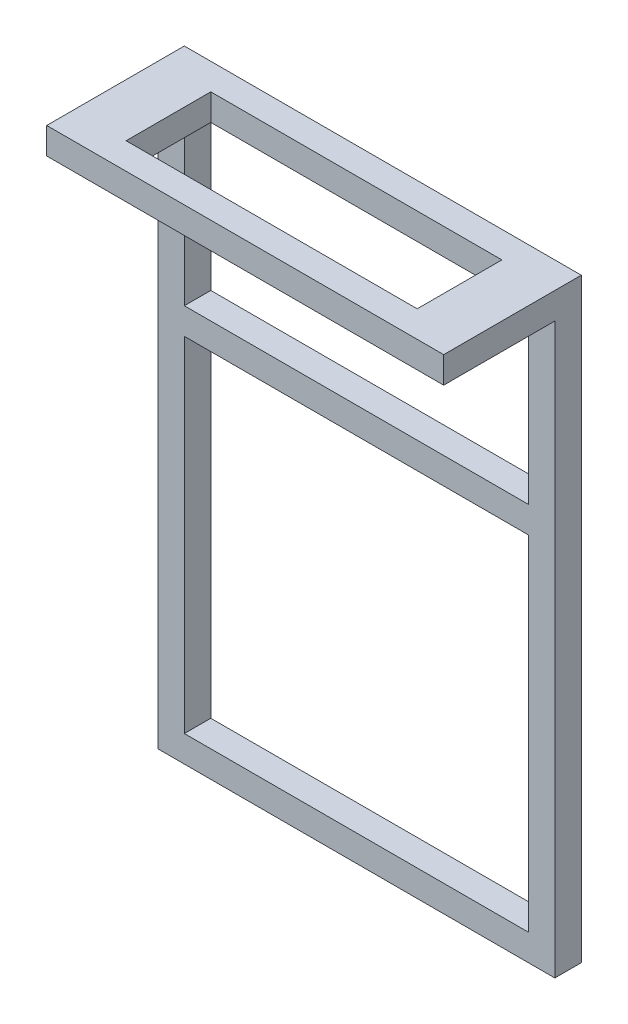
SolidWorks part; units mm, degrees
ref_plane "Front Plane" through (0, 0, 0) normal (0, 0, 1) x (1, 0, 0)
ref_plane "Top Plane" through (0, 0, 0) normal (0, 1, 0) x (1, 0, 0)
ref_plane "Right Plane" through (0, 0, 0) normal (1, 0, 0) x (0, 0, -1)
sketch "Sketch1" plane through (0, 0, 0) normal (0, 1, 0) x (1, 0, 0)
  line L1 (0, 0) -> (30, 0)
  line L2 (0, 0) -> (0, -10.4)
  line L3 (0, -10.4) -> (30, -10.4)
  line L4 (30, 0) -> (30, -10.4)
  dimension "D1" = 10.4
  dimension "D2" = 30
extrude "Boss-Extrude1" add sketch "Sketch1" along normal blind 2
sketch "Sketch2" plane through (0, 2, 0) normal (0, 1, 0) x (1, 0, 0)
  line L0 (0, 0) -> (0, -10.4) construction
  line L1 (4, -2) -> (26, -2)
  line L2 (4, -2) -> (4, -8.4)
  line L3 (4, -8.4) -> (26, -8.4)
  line L4 (26, -2) -> (26, -8.4)
  line L5 (30, -10.4) -> (30, 0) construction
  line L6 (30, 0) -> (0, 0) construction
  line L7 (0, -10.4) -> (30, -10.4) construction
  dimension "D1" = 4
  dimension "D2" = 4
  dimension "D3" = 2
  dimension "D4" = 2
extrude "Cut-Extrude1" cut sketch "Sketch2" against normal through all
sketch "Sketch4" plane through (0, 2, 0) normal (0, 1, 0) x (1, 0, 0)
  line L0 (30, -10.4) -> (30, 0) construction
  line L1 (0, 0) -> (30, 0)
  line L2 (0, 0) -> (0, -2)
  line L3 (0, -2) -> (30, -2)
  line L4 (30, 0) -> (30, -2)
  line L5 (26, -2) -> (4, -2) construction
extrude "Boss-Extrude2" add sketch "Sketch4" against normal blind 45
sketch "Sketch5" plane through (0, 0, 0) normal (0, 0, -1) x (-1, 0, 0)
  line L0 (-30, 2) -> (-30, -43) construction
  line L1 (-30, -13) -> (0, -13)
  line L2 (-30, -13) -> (-30, -43)
  line L3 (-30, -43) -> (0, -43)
  line L4 (0, -13) -> (0, -43)
  line L5 (-28, -15) -> (-28, -41)
  line L6 (-28, -41) -> (-2, -41)
  line L7 (-2, -15) -> (-2, -41)
  line L8 (-28, -15) -> (-2, -15)
  dimension "D1" = 30
  dimension "D2" = 2
extrude "Cut-Extrude3" cut sketch "Sketch5" against normal through all contours L8 L5 L6 L7
sketch "Sketch6" plane through (0, 0, 0) normal (0, 0, -1) x (-1, 0, 0)
  line L0 (-28, -15) -> (-2, -15) construction
  line L1 (-28, 0) -> (-2, 0)
  line L2 (-28, 0) -> (-28, -13)
  line L3 (-28, -13) -> (-2, -13)
  line L4 (-2, 0) -> (-2, -13)
  line L5 (-30, 2) -> (-30, -43) construction
  line L6 (-30, 2) -> (0, 2) construction
  line L7 (0, 2) -> (0, -43) construction
  dimension "D1" = 2
  dimension "D2" = 2
  dimension "D3" = 2
  dimension "D4" = 2
extrude "Cut-Extrude4" cut sketch "Sketch6" against normal through all
